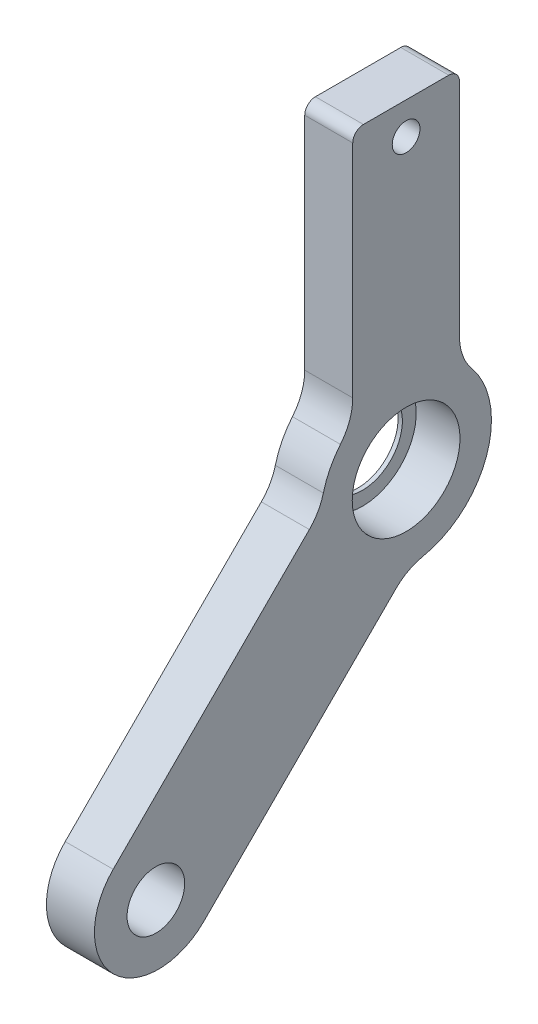
SolidWorks part; units mm, degrees
ref_plane "前视基准面" through (0, 0, 0) normal (0, 0, 1) x (1, 0, 0)
ref_plane "上视基准面" through (0, 0, 0) normal (0, 1, 0) x (1, 0, 0)
ref_plane "右视基准面" through (0, 0, 0) normal (1, 0, 0) x (0, 0, -1)
sketch "草图1" plane through (0, 0, 0) normal (-1, 0, 0) x (0, 0, 1)
  line L0 (-4, 30) -> (4, 30)
  line L2 (9.0672, -0.3462) -> (27.4519, -18.731)
  line L3 (5, 8.3066) -> (5, 29)
  line L5 (-5, 8.3066) -> (-5, 29)
  line L10 (0.9565, -9.2061) -> (18.9667, -27.2162)
  arc A0 (-6.1538, 5.1118) -> (-1.5871, -7.841) centre (0, 0) ccw
  arc A1 (7.7555, 1.9627) -> (6.1538, 5.1118) centre (0, 0) ccw
  arc A2 (27.4519, -18.731) -> (18.9667, -27.2162) centre (23.2093, -22.9736) cw
  circle A3 centre (0, 0) radius 3.75
  arc A4 (0.9565, -9.2061) -> (-1.5871, -7.841) centre (-2.579, -12.7416) ccw
  arc A5 (-5, 8.3066) -> (-6.1538, 5.1118) centre (-10, 8.3066) cw
  arc A6 (9.0672, -0.3462) -> (7.7555, 1.9627) centre (12.6027, 3.1894) cw
  arc A7 (5, 8.3066) -> (6.1538, 5.1118) centre (10, 8.3066) ccw
  arc A8 (5, 29) -> (4, 30) centre (4, 29) ccw
  arc A9 (-5, 29) -> (-4, 30) centre (-4, 29) cw
  circle A10 centre (0, 27) radius 1.3
  circle A11 centre (23.4521, -23.2164) radius 2.7
  point P3 (35.3553, -35.3553)
  point P5 (4, 1.6569)
  point P6 (38.1838, -32.5269)
  point P7 (5, 30)
  point P8 (-4, -1.6569)
  point P9 (32.5269, -38.1838)
  point P10 (-5, 30)
  point P19 (23.5839, -31.8335)
  point P22 (-0.2536, -7.996)
  point P25 (-5, 6.245)
  point P28 (7.9641, 0.7569)
  dimension "D1" = 16
  dimension "D3" = 33
  dimension "D6" = 5
  dimension "D7" = 5
  dimension "D8" = 1
  dimension "D9" = 10
  dimension "D10" = 6
  dimension "D11" = 135
  dimension "D12" = 5.4
  dimension "D13" = 7.5
  dimension "D14" = 2.6
  dimension "D15" = 27
  dimension "D2" = 30
  dimension "D4" = 12
extrude "凸台-拉伸1" add sketch "草图1" along normal mid plane 4.5
sketch "草图7" plane through (2.25, 0, 0) normal (-1, 0, 0) x (0, 0, 1)
  circle A0 centre (0, 0) radius 5.05
  dimension "D1" = 10.1
extrude "切除-拉伸4" cut sketch "草图7" along normal blind 4.1
